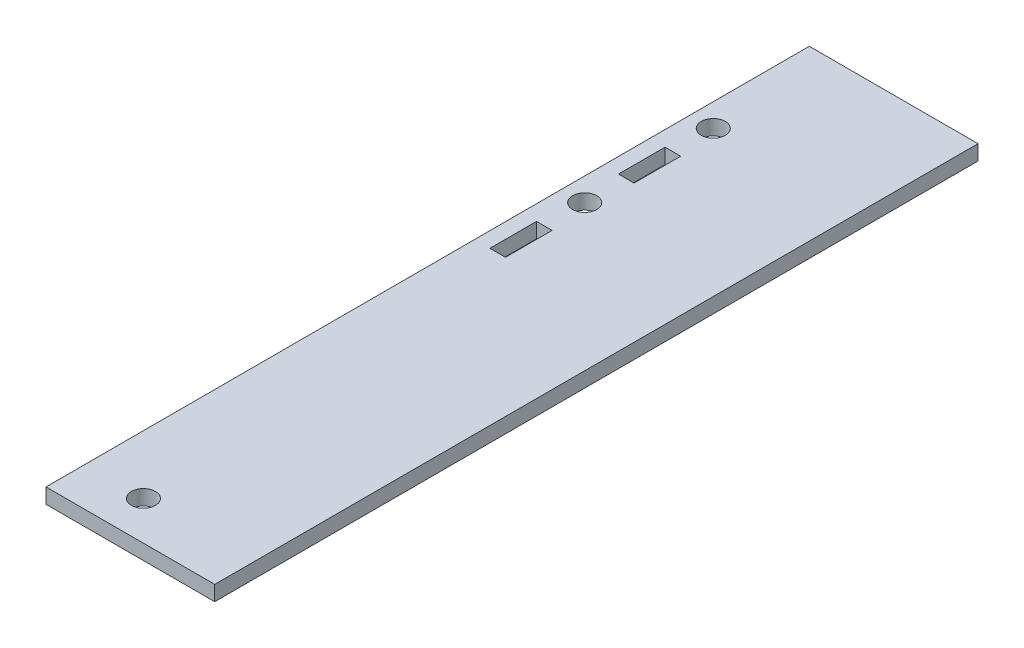
SolidWorks part; units mm, degrees
ref_plane "Front Plane" through (0, 0, 0) normal (0, 0, 1) x (1, 0, 0)
ref_plane "Top Plane" through (0, 0, 0) normal (0, 1, 0) x (1, 0, 0)
ref_plane "Right Plane" through (0, 0, 0) normal (1, 0, 0) x (0, 0, -1)
sketch "Sketch1" plane through (0, 0, 0) normal (0, 0, 1) x (1, 0, 0)
  line L0 (0, 0) -> (0, 2.3813)
  line L1 (0, 2.3813) -> (19.05, 2.3813)
  line L2 (19.05, 2.3813) -> (19.05, 0)
  line L3 (19.05, 0) -> (0, 0)
  dimension "D1" = 2.3813
  dimension "D2" = 19.05
extrude "Boss-Extrude1" add sketch "Sketch1" along normal blind 120.65
sketch "Sketch5" plane through (0, 2.3813, 0) normal (0, 1, 0) x (1, 0, 0)
  line L0 (16.6687, -25.2095) -> (19.05, -25.2095)
  line L2 (19.05, -120.65) -> (19.05, 0) construction
  line L3 (16.3176, -28.9877) -> (13.8449, -28.9877)
  line L10 (15.0813, -39.1478) -> (15.0813, -49.3078)
  line L11 (15.0813, -49.3078) -> (15.0813, -45.5295)
  line L17 (15.0813, -49.3078) -> (15.0813, -52.8955)
  line L24 (16.3176, -28.9877) -> (16.3176, -32.5755)
  line L25 (15.0813, -52.8955) -> (16.3176, -52.8955)
  line L26 (15.0813, -52.8955) -> (13.8449, -52.8955)
  line L27 (13.8449, -52.8955) -> (13.8449, -45.5295)
  line L28 (13.8449, -45.5295) -> (16.3176, -45.5295)
  line L29 (16.3176, -45.5295) -> (16.3176, -52.8955)
  line L30 (16.3176, -32.5755) -> (15.0813, -32.5755)
  line L31 (15.0813, -32.5755) -> (13.8449, -32.5755)
  line L32 (13.8449, -32.5755) -> (13.8449, -25.2095)
  line L33 (13.8449, -25.2095) -> (16.3176, -25.2095)
  line L34 (16.3176, -25.2095) -> (16.3176, -28.9877)
  circle A0 centre (15.0813, -39.1478) radius 1.905
  circle A3 centre (15.0813, -18.8277) radius 1.905
  dimension "D7" = 10.16
  dimension "D12" = 3.81
  dimension "D10" = 7.366
  dimension "D11" = 3.81
  dimension "D2" = 2.3813
  dimension "D3" = 3.5877
  dimension "D4" = 1.2363
  dimension "D5" = 1.2363
  dimension "D6" = 7.366
  dimension "D8" = 3.5878
  dimension "D9" = 1.2363
sketch "Sketch8" plane through (0, 2.3813, 0) normal (0, 1, 0) x (1, 0, 0)
  line L3 (0, 0) -> (0, -88.0829)
  line L4 (0, -120.65) -> (0, 0) construction
  line L5 (19.05, 0) -> (38.1, 0)
  line L6 (38.1, 0) -> (38.1, -120.65)
  line L7 (38.1, -120.65) -> (19.05, -120.65)
  line L9 (19.05, 0) -> (0, 0)
  line L10 (0, 0) -> (0, -120.65)
  line L11 (0, -120.65) -> (19.05, -120.65)
  line L12 (19.05, -120.65) -> (19.05, 0)
  line L13 (19.05, 0) -> (0, 0)
  line L14 (0, 0) -> (0, -88.0829)
  line L15 (0, -120.65) -> (19.05, -120.65)
  line L16 (19.05, -120.65) -> (19.05, 0)
  line M11 (19.05, -120.65) -> (19.05, 0)
  dimension "D2" = 19.05
  dimension "D1" = 0
extrude "Boss-Extrude3" add sketch "Sketch8" against normal blind 2.3813 contours L7 L6 L5 M11
sketch "Sketch9" plane through (0, 2.3813, 0) normal (0, 1, 0) x (1, 0, 0)
  circle A0 centre (20.701, -114.5159) radius 1.905
  dimension "D1" = 3.81
extrude "Cut-Extrude5" cut sketch "Sketch9" against normal through all
extrude "Cut-Extrude6" cut sketch "Sketch5" against normal blind 2.54
sketch "Sketch10" plane through (0, 2.3813, 0) normal (0, 1, 0) x (1, 0, 0)
  line L0 (0, 0) -> (0, 29.6545)
  line L1 (0, 29.6545) -> (38.1, 29.6545)
  line L2 (38.1, 29.6545) -> (38.1, 0)
  line L3 (38.1, 0) -> (0, 0)
  dimension "D1" = 29.6545
extrude "Boss-Extrude4" add sketch "Sketch10" against normal blind 2.3813
sketch "Sketch11" plane through (0, 0, 0) normal (0, -1, 0) x (1, 0, 0)
  line L5 (15.0813, -11.6523) -> (16.3176, -11.6523)
sketch "Sketch12" plane through (0, 2.3813, 0) normal (0, 1, 0) x (1, 0, 0)
  line L0 (0, -120.65) -> (11.43, -120.65)
  line L2 (38.1, -120.65) -> (0, -120.65) construction
  line L3 (11.43, -120.65) -> (11.43, 29.6545)
  line L4 (38.1, 29.6545) -> (0, 29.6545) construction
  line L5 (11.43, 29.6545) -> (0, 29.6545)
  line L6 (0, 29.6545) -> (0, -120.65)
  dimension "D1" = 11.43
extrude "Cut-Extrude8" cut sketch "Sketch12" against normal through all
sketch "Sketch13" plane through (0, 2.3813, 0) normal (0, 1, 0) x (1, 0, 0)
  line L0 (11.43, 29.6545) -> (11.43, 0)
  line L1 (11.43, -120.65) -> (11.43, 29.6545) construction
  line L2 (11.43, 0) -> (38.1, 0)
  line L3 (38.1, 29.6545) -> (38.1, -120.65) construction
  line L4 (38.1, 0) -> (38.1, 29.6545)
  line L5 (38.1, 29.6545) -> (11.43, 29.6545)
extrude "Cut-Extrude9" cut sketch "Sketch13" against normal through all
